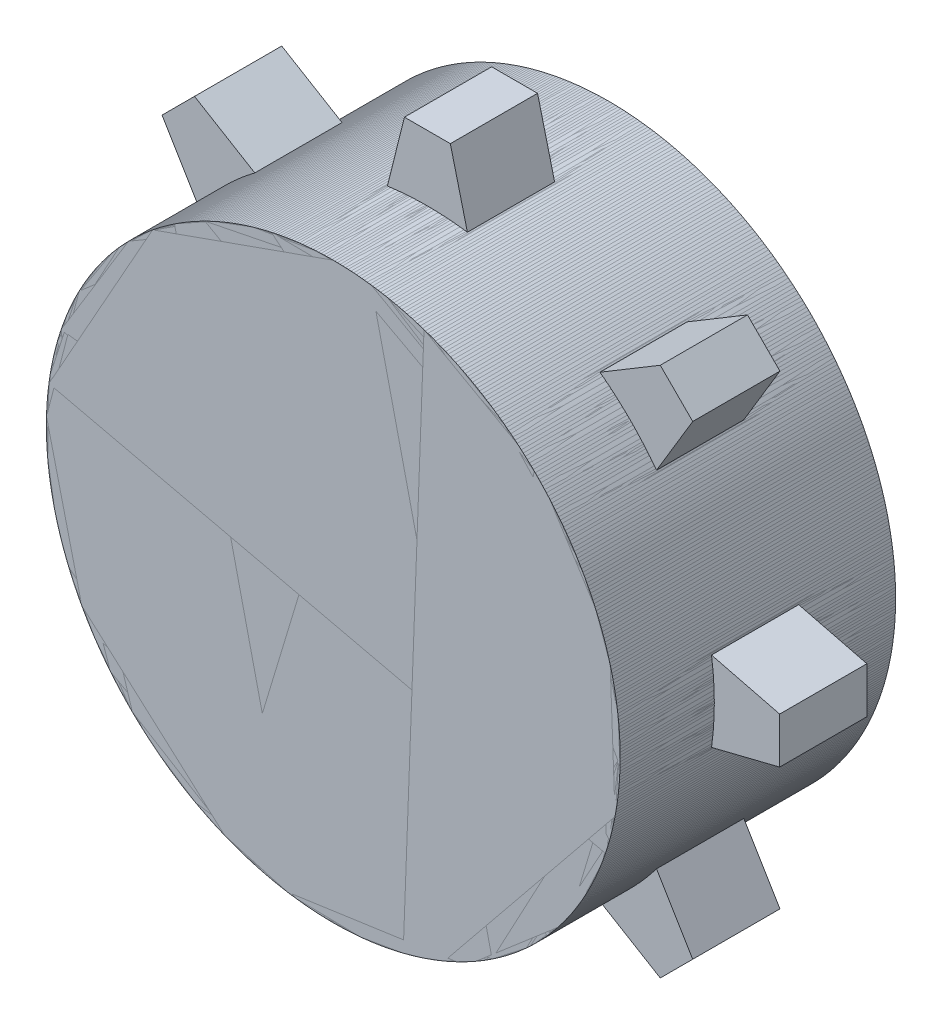
SolidWorks part; units mm, degrees
other "Markup1"
sketch "Sketch4" plane through (-30, 25, -15) normal (-0.7934, 0.0966, -0.601) x (-0.1502, -0.9879, 0.0395)
ref_plane "Front Plane" through (0, 0, 0) normal (0, 0, 1) x (1, 0, 0)
ref_plane "Top Plane" through (0, 0, 0) normal (0, 1, 0) x (1, 0, 0)
ref_plane "Right Plane" through (0, 0, 0) normal (1, 0, 0) x (0, 0, -1)
sketch "Sketch1" plane through (0, 0, 0) normal (0, 0, 1) x (1, 0, 0)
  line L0 (0, 0) -> (-50000, 0) construction
  circle A0 centre (0, 0) radius 31.25
  dimension "D1" = 62.5
extrude "Boss-Extrude1" add sketch "Sketch1" along normal mid plane 30
sketch "Sketch2" plane through (0, 0, 0) normal (0, 0, 1) x (1, 0, 0)
  line L0 (10.9478, 0) -> (-49989.0522, 0) construction
  line L1 (-28.3721, -5) -> (-28.3721, 5)
  line L2 (-28.3721, -5) -> (-38.3721, -2.5)
  line L3 (-28.3721, 5) -> (-38.3721, 2.5)
  line L4 (-38.3721, 2.5) -> (-38.3721, -2.5)
  line L5 (-33.6569, -15.7864) -> (-33.0873, 15.7864) construction
  point P6 (-28.3721, 0)
  point P13 (-33.3721, 0)
  dimension "D3" = 5
  dimension "D1" = 10
  dimension "D2" = 10
  dimension "D4" = 5
extrude "Boss-Extrude2" add sketch "Sketch2" along normal mid plane 9.5
sketch "Sketch8" plane through (0, 0, -15) normal (0, 0, -1) x (-1, 0, 0)
  line L0 (38.3721, 2.5) -> (38.3721, -2.5) construction
  line L1 (38.3721, 4.3667) -> (36.1221, 4.3667)
  line L2 (38.3721, 4.3667) -> (38.3721, -4.3553)
  line L3 (38.3721, -4.3553) -> (36.1221, -4.3553)
  line L4 (36.1221, 4.3667) -> (36.1221, -4.3553)
  dimension "D1" = 2.25
extrude "Cut-Extrude5" [suppressed] cut sketch "Sketch8" against normal blind 31
fillet "Fillet1" [suppressed] radius 1
ref_plane "Plane2" through (0, 0, 0) normal (0, 1, 0) x (1, 0, 0)
pattern_circular "CirPattern1" count 8 over 360 about axis through (0, 0, 0) along (0, 0, 1) of bodies 102 108
sketch "Sketch3" plane through (0, 0, 15) normal (0, 0, 1) x (1, 0, 0)
  line L0 (5.5, 5.5) -> (-5.5, 5.5) construction
  line L5 (-5.5, 5.5) -> (5.5, -5.5) construction
  line L6 (-5.5, -5.5) -> (5.5, 5.5) construction
  line L7 (-5.5, 5.5) -> (-5.5, -5.5) construction
  line L8 (5.5, 5.5) -> (5.5, -5.5) construction
  line L9 (5.5, -5.5) -> (-5.5, -5.5) construction
  circle A0 centre (0, 0) radius 2.5
  circle A1 centre (5.5, 5.5) radius 2
  circle A2 centre (-5.5, 5.5) radius 2
  circle A3 centre (-5.5, -5.5) radius 2
  circle A4 centre (5.5, -5.5) radius 2
  dimension "D1" = 5
  dimension "D4" = 4
  dimension "D5" = 4
  dimension "D6" = 4
  dimension "D7" = 4
  dimension "D2" = 11
  dimension "D3" = 11
extrude "Cut-Extrude6" [suppressed] cut sketch "Sketch3" against normal blind 10
ref_point "Point1" [suppressed]
